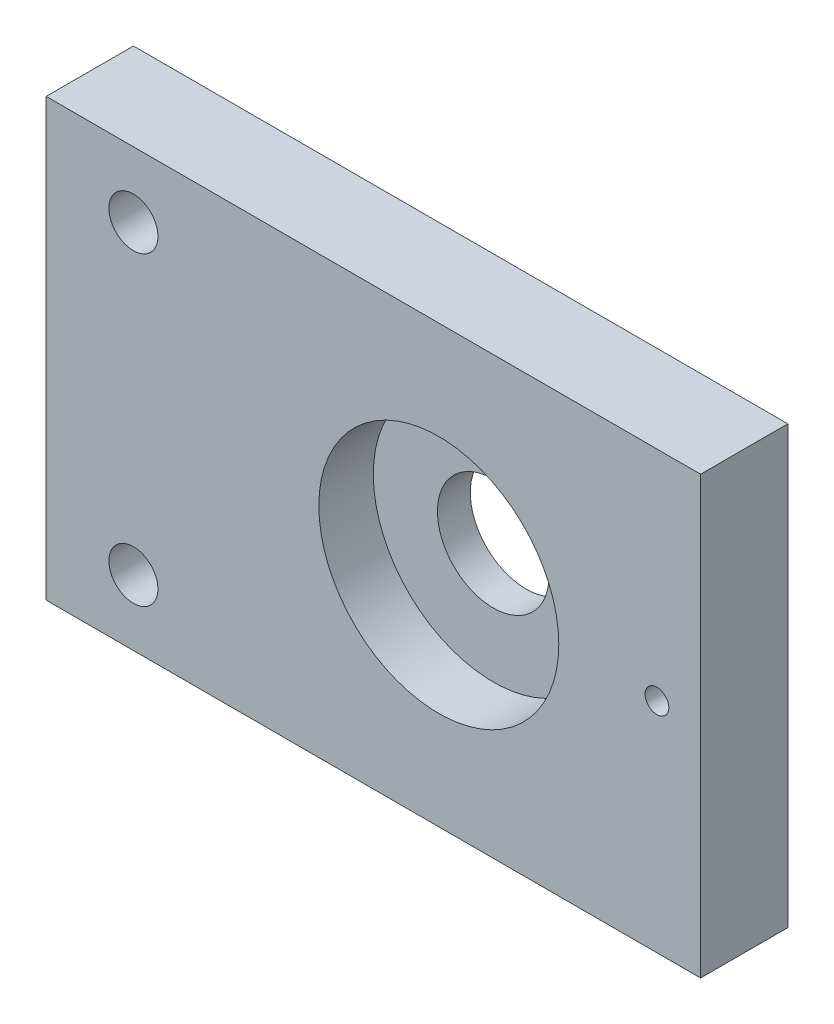
SolidWorks part; units mm, degrees
material "6061-T6 Al"
ref_plane "Front Plane" through (0, 0, 0) normal (0, 0, 1) x (1, 0, 0)
ref_plane "Top Plane" through (0, 0, 0) normal (0, 1, 0) x (1, 0, 0)
ref_plane "Right Plane" through (0, 0, 0) normal (1, 0, 0) x (0, 0, -1)
sketch "Sketch1" plane through (0, 0, 0) normal (0, 0, 1) x (1, 0, 0)
  line L1 (0, 0) -> (95.25, 0)
  line L2 (0, 0) -> (0, 63.5)
  line L3 (0, 63.5) -> (95.25, 63.5)
  line L4 (95.25, 0) -> (95.25, 63.5)
  dimension "D1" = 63.5
  dimension "D2" = 95.25
extrude "Boss-Extrude1" add sketch "Sketch1" along normal blind 12.7
hole_wizard "CBORE for 1/4 Socket Head Cap Screw1" positions "Sketch4" profile "Sketch3" counterbore size "1/4" standard "Ansi Inch" end condition through all
sketch "Sketch4" plane through (0, 0, 0) normal (0, 0, -1) x (-1, 0, 0)
  line L0 (-12.7, 9.525) -> (-12.7, 53.975) construction
  line L1 (0, 63.5) -> (0, 0) construction
  line L4 (0, 31.75) -> (-12.7, 31.75) construction
  line L5 (0, 63.5) -> (0, 0) construction
  point P0 (-12.7, 53.975)
  point P1 (-12.7, 9.525)
  dimension "D1" = 12.7
  dimension "D2" = 44.45
sketch "Sketch3" plane through (12.7, 53.975, 0) normal (1, 0, 0) x (0, 1, 0)
  line L0 (0, 0) -> (0, 12.7)
  line L1 (0, 12.7) -> (3.5712, 12.7)
  line L3 (3.5712, 12.7) -> (3.5712, 6.35)
  line L4 (3.5712, 6.35) -> (5.5562, 6.35)
  line L5 (5.5562, 6.35) -> (5.5562, 0)
  line L7 (5.5562, 0) -> (0, 0)
  line L11 (0, -6.35) -> (0, 107.95) construction
  dimension "Thru Hole Dia." = 7.1425
  dimension "Thru Hole Depth" = 12.7
  dimension "C'Bore Dia." = 11.1125
  dimension "C'Bore Depth" = 6.35
hole_wizard "CBORE for 5/8 Socket Head Cap Screw1" positions "Sketch6" profile "Sketch5" counterbore size "5/8" standard "Ansi Inch" end condition through all
sketch "Sketch6" plane through (0, 0, 12.7) normal (0, 0, 1) x (1, 0, 0)
  line L0 (95.25, 0) -> (95.25, 63.5) construction
  line L3 (95.25, 31.75) -> (57.15, 31.75) construction
  line L4 (95.25, 0) -> (95.25, 63.5) construction
  point P0 (57.15, 31.75)
  dimension "D1" = 38.1
sketch "Sketch5" plane through (57.15, 31.75, 12.7) normal (1, 0, 0) x (0, -1, 0)
  line L0 (0, 0) -> (0, 12.7)
  line L1 (0, 12.7) -> (8.128, 12.7)
  line L3 (8.128, 12.7) -> (8.128, 7.9248)
  line L4 (8.128, 7.9248) -> (17.4625, 7.9248)
  line L5 (17.4625, 7.9248) -> (17.4625, 0)
  line L7 (17.4625, 0) -> (0, 0)
  line L11 (0, -6.35) -> (0, 107.95) construction
  dimension "Thru Hole Dia." = 16.256
  dimension "Thru Hole Depth" = 12.7
  dimension "C'Bore Dia." = 34.925
  dimension "C'Bore Depth" = 7.9248
hole_wizard "#8-32 Tapped Hole1" positions "Sketch8" profile "Sketch7" tap size "#8-32" standard "Ansi Inch" end condition through all
sketch "Sketch8" plane through (0, 0, 12.7) normal (0, 0, 1) x (1, 0, 0)
  line L0 (57.15, 31.75) -> (88.9, 31.75) construction
  point P0 (88.9, 31.75)
  dimension "D1" = 31.75
sketch "Sketch7" plane through (88.9, 31.75, 12.7) normal (1, 0, 0) x (0, -1, 0)
  line L0 (0, 0) -> (0, 12.7)
  line L1 (0, 12.7) -> (1.7272, 12.7)
  line L2 (1.7272, 12.7) -> (1.7272, 0)
  line L5 (1.7272, 0) -> (0, 0)
  line L11 (0, -6.35) -> (0, 107.95) construction
  dimension "Thru Tap Drill Dia." = 3.4544
  dimension "Thru Tap Drill Depth" = 12.7
cosmetic thread "Hole Thread1" parameters "D2"=4.1656
